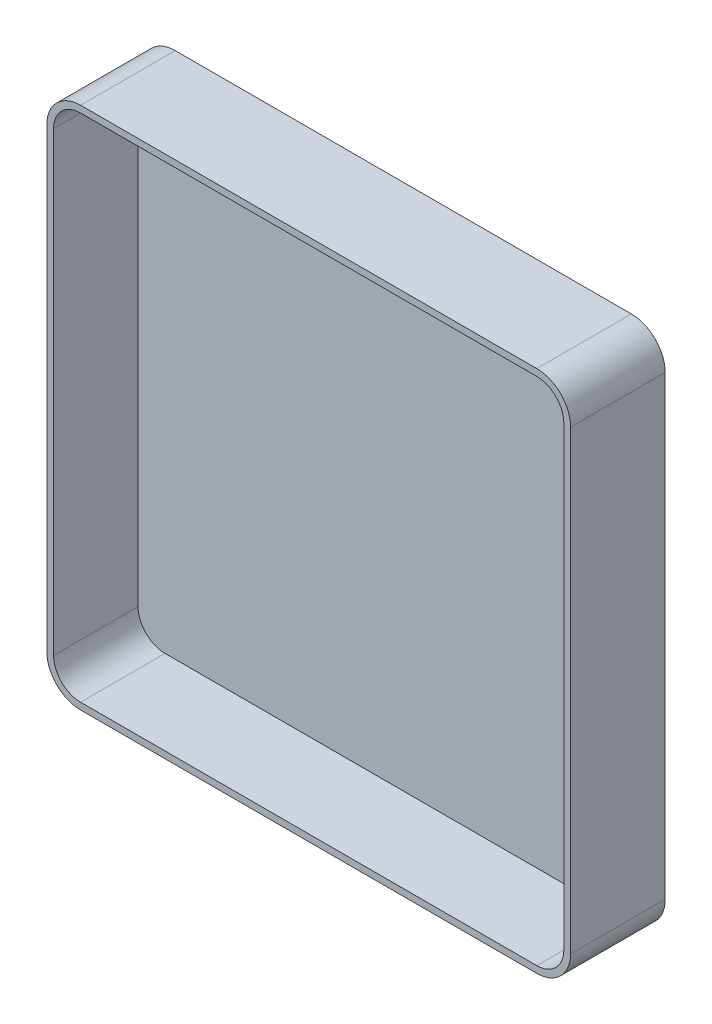
SolidWorks part; units mm, degrees
ref_plane "前视基准面" through (0, 0, 0) normal (0, 0, 1) x (1, 0, 0)
ref_plane "上视基准面" through (0, 0, 0) normal (0, 1, 0) x (1, 0, 0)
ref_plane "右视基准面" through (0, 0, 0) normal (1, 0, 0) x (0, 0, -1)
other "Configuration Table"
sketch "草图1" plane through (0, 0, 0) normal (0, 0, 1) x (1, 0, 0)
  line L0 (404.3012, -319.7559) -> (404.3012, 500.2441) construction
  line L1 (404.3012, -319.7559) -> (404.3012, 500.2441) construction
  line L3 (414.3012, 12.7441) -> (549.3012, 12.7441)
  line L4 (404.3012, 22.7441) -> (404.3012, 157.7441)
  line L5 (414.3012, 167.7441) -> (549.3012, 167.7441)
  line L6 (559.3012, 22.7441) -> (559.3012, 157.7441)
  line L7 (544.3012, 90.2441) -> (559.3012, 90.2441) construction
  line L8 (481.8012, 167.7441) -> (481.8012, 12.7441) construction
  arc A0 (544.3012, 87.7441) -> (544.3012, 92.7441) centre (544.3012, 90.2441) ccw construction
  arc A1 (544.3012, 87.7441) -> (544.3012, 92.7441) centre (544.3012, 90.2441) ccw construction
  arc A2 (549.3012, 12.7441) -> (559.3012, 22.7441) centre (549.3012, 22.7441) ccw
  arc A3 (414.3012, 12.7441) -> (404.3012, 22.7441) centre (414.3012, 22.7441) cw
  arc A4 (414.3012, 167.7441) -> (404.3012, 157.7441) centre (414.3012, 157.7441) ccw
  arc A5 (549.3012, 167.7441) -> (559.3012, 157.7441) centre (549.3012, 157.7441) cw
  point P3 (0, 0)
  dimension "D2" = 20
  dimension "D1" = 155
  dimension "D4" = 77.5
extrude "凸台-拉伸1" add sketch "草图1" along normal blind 3
sketch "草图2" plane through (0, 0, 3) normal (0, 0, 1) x (1, 0, 0)
  line L0 (557.3012, 22.7441) -> (557.3012, 157.7441)
  line L1 (549.3012, 165.7441) -> (414.3012, 165.7441)
  line L2 (406.3012, 157.7441) -> (406.3012, 22.7441)
  line L3 (414.3012, 14.7441) -> (549.3012, 14.7441)
  line L4 (414.3012, 12.7441) -> (549.3012, 12.7441)
  line L5 (559.3012, 22.7441) -> (559.3012, 157.7441)
  line L6 (549.3012, 167.7441) -> (414.3012, 167.7441)
  line L7 (404.3012, 157.7441) -> (404.3012, 22.7441)
  line L8 (414.3012, 12.7441) -> (549.3012, 12.7441)
  line L9 (559.3012, 22.7441) -> (559.3012, 157.7441)
  line L10 (549.3012, 167.7441) -> (414.3012, 167.7441)
  line L11 (404.3012, 157.7441) -> (404.3012, 22.7441)
  arc A0 (557.3012, 157.7441) -> (549.3012, 165.7441) centre (549.3012, 157.7441) ccw
  arc A1 (414.3012, 165.7441) -> (406.3012, 157.7441) centre (414.3012, 157.7441) ccw
  arc A2 (406.3012, 22.7441) -> (414.3012, 14.7441) centre (414.3012, 22.7441) ccw
  arc A3 (549.3012, 14.7441) -> (557.3012, 22.7441) centre (549.3012, 22.7441) ccw
  arc A4 (404.3012, 22.7441) -> (414.3012, 12.7441) centre (414.3012, 22.7441) ccw
  arc A5 (549.3012, 12.7441) -> (559.3012, 22.7441) centre (549.3012, 22.7441) ccw
  arc A6 (559.3012, 157.7441) -> (549.3012, 167.7441) centre (549.3012, 157.7441) ccw
  arc A7 (414.3012, 167.7441) -> (404.3012, 157.7441) centre (414.3012, 157.7441) ccw
  arc A8 (404.3012, 22.7441) -> (414.3012, 12.7441) centre (414.3012, 22.7441) ccw
  arc A9 (549.3012, 12.7441) -> (559.3012, 22.7441) centre (549.3012, 22.7441) ccw
  arc A10 (559.3012, 157.7441) -> (549.3012, 167.7441) centre (549.3012, 157.7441) ccw
  arc A11 (414.3012, 167.7441) -> (404.3012, 157.7441) centre (414.3012, 157.7441) ccw
  dimension "D1" = 0
  dimension "D2" = 2
extrude "凸台-拉伸2" add sketch "草图2" along normal blind 25
